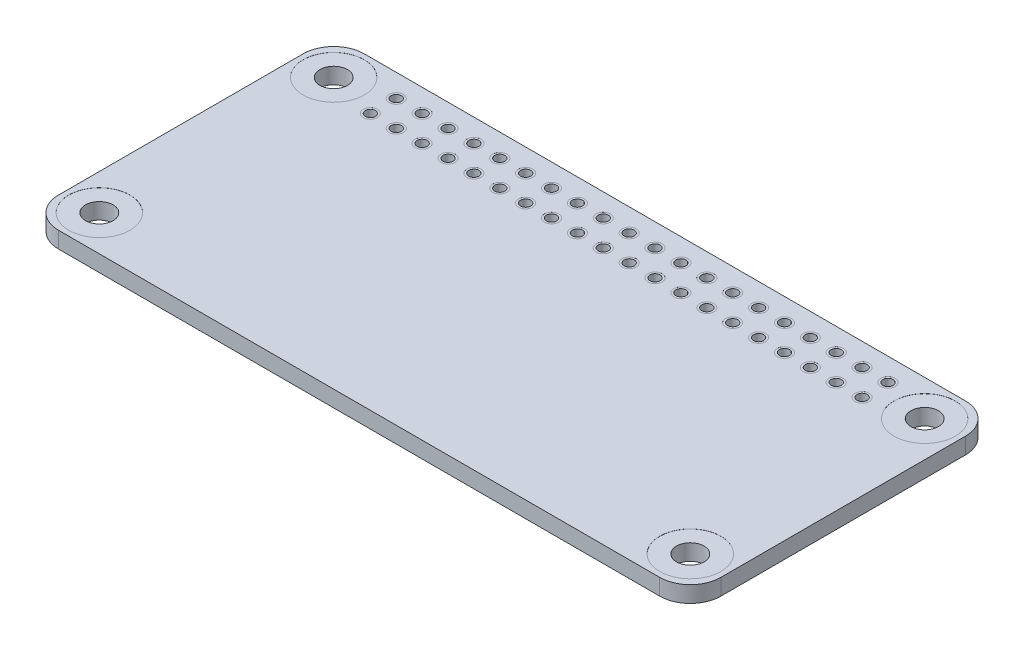
SolidWorks part; units mm, degrees
material "Silicon"
ref_plane "Front Plane" through (0, 0, 0) normal (0, 0, 1) x (1, 0, 0)
ref_plane "Top Plane" through (0, 0, 0) normal (0, 1, 0) x (1, 0, 0)
ref_plane "Right Plane" through (0, 0, 0) normal (1, 0, 0) x (0, 0, -1)
sketch "BaseS" plane through (0, 0, 0) normal (0, 1, 0) x (1, 0, 0)
  line L1 (-32.5, 15) -> (32.5, 15)
  line L2 (-32.5, 15) -> (-32.5, -15)
  line L3 (-32.5, -15) -> (32.5, -15)
  line L4 (32.5, 15) -> (32.5, -15)
  line L5 (-32.5, 15) -> (32.5, -15) construction
  line L6 (-32.5, -15) -> (32.5, 15) construction
  point P0 (0, 0)
  dimension "Width" = 30
  dimension "Length" = 65
extrude "Base" add sketch "BaseS" along normal mid plane 1.6
hole_wizard "M2.5 Clearance Hole" positions "Sketch2" profile "Sketch3" hole size "M2.5" standard "ANSI Metric" end condition through all
sketch "Sketch2" plane through (0, 0.8, 0) normal (0, 1, 0) x (1, 0, 0)
  line L0 (-29, 11.5) -> (-29, -11.5) construction
  line L2 (-32.5, 15) -> (-32.5, -15) construction
  line L3 (32.5, 15) -> (-32.5, 15) construction
  line L4 (-32.5, -15) -> (32.5, -15) construction
  point P0 (-29, 11.5)
  point P2 (-29, -11.5)
  dimension "XDim" = 3.5
  dimension "YDim" = 3.5
  dimension "D3" = 3.5
sketch "Sketch3" plane through (-29, 0.8, -11.5) normal (1, 0, 0) x (0, 0, 1)
  line L0 (0, 0) -> (0, 1.6)
  line L1 (0, 1.6) -> (1.35, 1.6)
  line L2 (1.35, 1.6) -> (1.35, 0)
  line L5 (1.35, 0) -> (0, 0)
  line L11 (0, -6.35) -> (0, 107.95) construction
  dimension "Thru Hole Dia." = 2.7
  dimension "Thru Hole Depth" = 1.6
sketch "FastenerAreaS" plane through (0, 0.8, 0) normal (0, 1, 0) x (1, 0, 0)
  line L0 (-29, -8.5) -> (-29, -15) construction
  line L1 (-32.5, -15) -> (32.5, -15) construction
  circle A0 centre (-29, -11.5) radius 3
  circle A1 centre (-29, -11.5) radius 1.35 construction
  circle A2 centre (-29, -11.5) radius 1.35
  circle A3 centre (-29, 11.5) radius 1.35 construction
  circle A4 centre (-29, 11.5) radius 1.35
  circle A5 centre (-29, 11.5) radius 3
  dimension "RefDia" = 6
  dimension "DiaControl" = 1.65
  dimension "RefWidthMountingTab" = 6.5
extrude "FastenerArea" cut sketch "FastenerAreaS" against normal blind 0.01
mirror "VM FA" about plane through (0, 0, 0) normal (0, 1, 0) of "FastenerArea"
hole_wizard "Ø1.0 (1) Diameter Hole IO" positions "Sketch7" profile "Sketch8" hole size "Ø1.0" standard "ANSI Metric" end condition through all
sketch "Sketch7" plane through (0, 0.8, 0) normal (0, 1, 0) x (1, 0, 0)
  circle A0 centre (-29, 11.5) radius 1.35 construction
  point P0 (-24.13, 12.77)
  dimension "YDim" = 1.27
  dimension "XDim" = 4.87
sketch "Sketch8" plane through (-24.13, 0.8, -12.77) normal (1, 0, 0) x (0, 0, 1)
  line L0 (0, 0) -> (0, 1.6)
  line L1 (0, 1.6) -> (0.5, 1.6)
  line L2 (0.5, 1.6) -> (0.5, 0)
  line L5 (0.5, 0) -> (0, 0)
  line L11 (0, -6.35) -> (0, 107.95) construction
  dimension "Thru Hole Dia." = 1
  dimension "Thru Hole Depth" = 1.6
sketch "SolderConnectionCutS" plane through (0, 0.8, 0) normal (0, 1, 0) x (1, 0, 0)
  circle A0 centre (-24.13, 12.77) radius 0.7
  circle A1 centre (-24.13, 12.77) radius 0.5 construction
  circle A2 centre (-24.13, 12.77) radius 0.5
  dimension "RefDia" = 1.4
  dimension "OffsetDiaControl" = 0.2
extrude "SolderConnectionCut" cut sketch "SolderConnectionCutS" against normal blind 0.001
mirror "SCCVM" about plane through (0, 0, 0) normal (0, 1, 0) of "SolderConnectionCut"
pattern_linear "LP DiaHole IO" count 20 spacing 2.54 along (1, 0, 0) count 2 spacing 2.54 along (0, 0, 1) of "Ø1.0 (1) Diameter Hole IO", "SolderConnectionCut", "SCCVM"
sketch "RefDimIO" plane through (0, 0.8, 0) normal (0, 1, 0) x (1, 0, 0)
  line L0 (-32.5, 15) -> (-32.5, -15) construction
  line L2 (-24.13, 12.77) -> (24.13, 12.77) construction
  line L3 (-24.13, 12.77) -> (-24.13, 10.23) construction
  line L4 (-24.13, 10.23) -> (24.13, 10.23) construction
  line L5 (24.13, 12.77) -> (24.13, 10.23) construction
  line L6 (-24.13, 12.77) -> (24.13, 10.23) construction
  line L7 (-24.13, 10.23) -> (24.13, 12.77) construction
  line L8 (32.5, 15) -> (-32.5, 15) construction
  point P0 (0, 11.5)
  dimension "XDim" = 32.5
  dimension "YDim" = 3.5
fillet "CornerRadius" radius 3 4 edges at (32.5, 0, -15) (32.5, 0, 15) (-32.5, 0, -15) (-32.5, 0, 15)
mirror "FCHM" about plane through (0, 0, 0) normal (1, 0, 0) of "VM FA", "FastenerArea", "M2.5 Clearance Hole"
